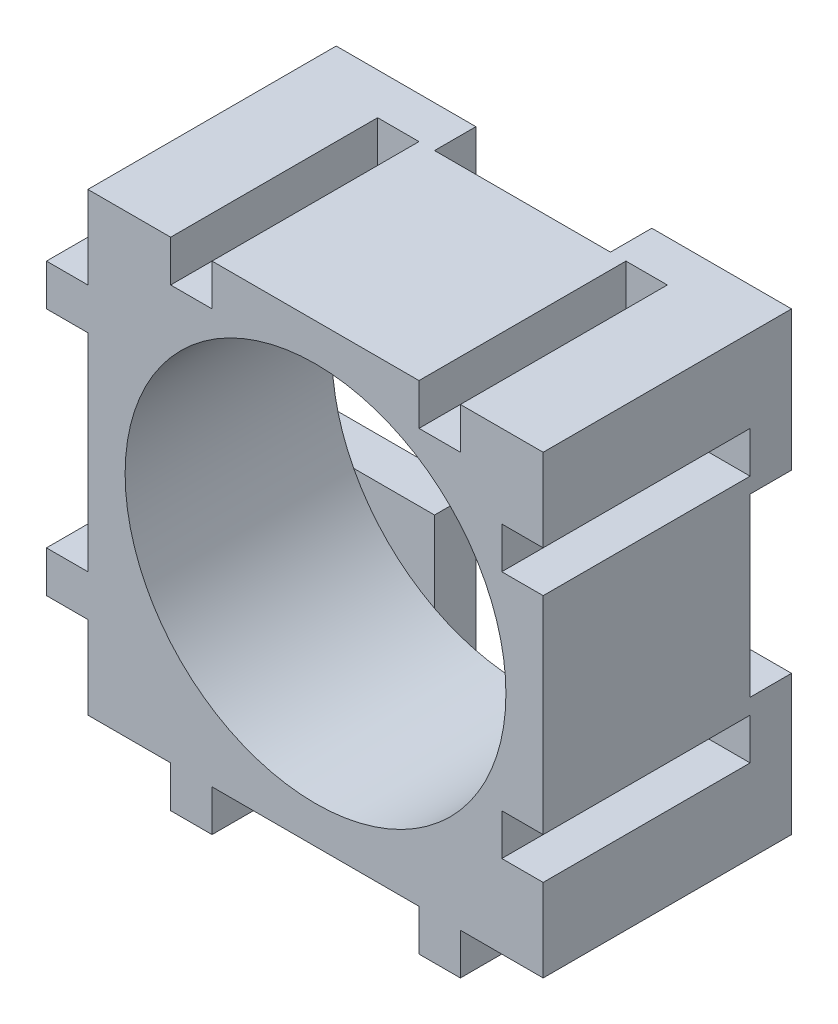
SolidWorks part; units mm, degrees
material "ABS"
ref_plane "Front Plane" through (0, 0, 0) normal (0, 0, 1) x (1, 0, 0)
ref_plane "Top Plane" through (0, 0, 0) normal (0, 1, 0) x (1, 0, 0)
ref_plane "Right Plane" through (0, 0, 0) normal (1, 0, 0) x (0, 0, -1)
sketch "Sketch1" plane through (0, 0, 0) normal (0, 0, 1) x (1, 0, 0)
  line L1 (-9.3991, 9.2441) -> (12.6009, 9.2441)
  line L2 (-9.3991, 9.2441) -> (-9.3991, -12.7559)
  line L3 (-9.3991, -12.7559) -> (12.6009, -12.7559)
  line L4 (12.6009, 9.2441) -> (12.6009, -12.7559)
  dimension "D1" = 22
  dimension "D2" = 22
extrude "Boss-Extrude1" add sketch "Sketch1" along normal blind 10
sketch "Sketch3" plane through (0, -12.7559, 0) normal (0, -1, 0) x (1, 0, 0)
  line L0 (-9.3991, 0) -> (12.6009, 0) construction
  line L1 (8.6009, 0) -> (6.6009, 0)
  line L2 (8.6009, 0) -> (8.6009, 10)
  line L3 (8.6009, 10) -> (6.6009, 10)
  line L4 (6.6009, 0) -> (6.6009, 10)
  line L5 (-9.3991, 10) -> (12.6009, 10) construction
  line L6 (-9.3991, 10) -> (-9.3991, 0) construction
  line L7 (-3.3991, 0) -> (-5.3991, 0)
  line L8 (-3.3991, 0) -> (-3.3991, 10)
  line L9 (-3.3991, 10) -> (-5.3991, 10)
  line L10 (-5.3991, 0) -> (-5.3991, 10)
  dimension "D1" = 2
  dimension "D2" = 2
  dimension "D3" = 10
  dimension "D4" = 4
extrude "Boss-Extrude2" add sketch "Sketch3" along normal blind 2
sketch "Sketch4" plane through (-9.3991, 0, 0) normal (-1, 0, 0) x (0, 0, 1)
  line L0 (0, 9.2441) -> (0, -12.7559) construction
  line L1 (0, 5.2441) -> (10, 5.2441)
  line L2 (0, 5.2441) -> (0, 3.2441)
  line L3 (0, 3.2441) -> (10, 3.2441)
  line L4 (10, 5.2441) -> (10, 3.2441)
  line L5 (10, 9.2441) -> (10, -12.7559) construction
  line L7 (0, -8.7559) -> (10, -8.7559)
  line L8 (0, -8.7559) -> (0, -6.7559)
  line L9 (0, -6.7559) -> (10, -6.7559)
  line L10 (10, -8.7559) -> (10, -6.7559)
  line L11 (10, 9.2441) -> (0, 9.2441) construction
  dimension "D1" = 10
  dimension "D2" = 4
  dimension "D3" = 2
  dimension "D4" = 2
extrude "Boss-Extrude3" add sketch "Sketch4" along normal blind 2
sketch "Sketch5" plane through (12.6009, 0, 0) normal (1, 0, 0) x (0, 0, -1)
  line L0 (0, -12.7559) -> (0, 9.2441) construction
  line L1 (0, 5.2441) -> (-10, 5.2441)
  line L2 (0, 5.2441) -> (0, 3.2441)
  line L3 (0, 3.2441) -> (-10, 3.2441)
  line L4 (-10, 5.2441) -> (-10, 3.2441)
  line L5 (-10, -12.7559) -> (-10, 9.2441) construction
  line L6 (-10, -12.7559) -> (0, -12.7559) construction
  line L7 (0, -6.7559) -> (-10, -6.7559)
  line L8 (0, -6.7559) -> (0, -8.7559)
  line L9 (0, -8.7559) -> (-10, -8.7559)
  line L10 (-10, -6.7559) -> (-10, -8.7559)
  dimension "D1" = 2
  dimension "D2" = 2
  dimension "D3" = 10
  dimension "D4" = 4
extrude "Cut-Extrude1" cut sketch "Sketch5" against normal blind 2
sketch "Sketch6" plane through (0, 9.2441, 0) normal (0, 1, 0) x (1, 0, 0)
  line L0 (12.6009, 0) -> (-9.3991, 0) construction
  line L1 (-5.3991, 0) -> (-3.3991, 0)
  line L2 (-5.3991, 0) -> (-5.3991, -10)
  line L3 (-5.3991, -10) -> (-3.3991, -10)
  line L4 (-3.3991, 0) -> (-3.3991, -10)
  line L5 (12.6009, -10) -> (-9.3991, -10) construction
  line L6 (12.6009, -10) -> (12.6009, 0) construction
  line L7 (6.6009, 0) -> (8.6009, 0)
  line L8 (6.6009, 0) -> (6.6009, -10)
  line L9 (6.6009, -10) -> (8.6009, -10)
  line L10 (8.6009, 0) -> (8.6009, -10)
  dimension "D1" = 2
  dimension "D2" = 2
  dimension "D3" = 10
  dimension "D4" = 4
extrude "Cut-Extrude2" cut sketch "Sketch6" against normal blind 2
sketch "Sketch7" plane through (0, 0, 10) normal (0, 0, 1) x (1, 0, 0)
  line L0 (12.6009, -6.7559) -> (12.6009, 3.2441) construction
  line L1 (-3.3991, -12.7559) -> (6.6009, -12.7559) construction
  circle A0 centre (1.6009, -1.7559) radius 9.2
  dimension "D1" = 18.4
  dimension "D3" = 11
  dimension "D2" = 11
extrude "Cut-Extrude3" cut sketch "Sketch7" against normal through all
sketch "Sketch8" plane through (0, 0, 0) normal (0, 0, -1) x (-1, 0, 0)
  line L1 (9.3991, 9.2441) -> (2.6491, 9.2441)
  line L2 (9.3991, 9.2441) -> (9.3991, 2.4941)
  line L3 (9.3991, 2.4941) -> (2.6491, 2.4941)
  line L4 (2.6491, 9.2441) -> (2.6491, 2.4941)
  line L5 (-12.6009, 9.2441) -> (-5.8509, 9.2441)
  line L6 (-12.6009, 9.2441) -> (-12.6009, 2.4941)
  line L7 (-12.6009, 2.4941) -> (-5.8509, 2.4941)
  line L8 (-5.8509, 9.2441) -> (-5.8509, 2.4941)
  line L9 (-12.6009, -12.7559) -> (-5.8509, -12.7559)
  line L10 (-12.6009, -12.7559) -> (-12.6009, -6.0059)
  line L11 (-12.6009, -6.0059) -> (-5.8509, -6.0059)
  line L12 (-5.8509, -12.7559) -> (-5.8509, -6.0059)
  line L13 (9.3991, -12.7559) -> (2.6491, -12.7559)
  line L14 (9.3991, -12.7559) -> (9.3991, -6.0059)
  line L15 (9.3991, -6.0059) -> (2.6491, -6.0059)
  line L16 (2.6491, -12.7559) -> (2.6491, -6.0059)
  dimension "D1" = 8.5
  dimension "D2" = 6.75
  dimension "D3" = 6.75
  dimension "D4" = 6.75
  dimension "D5" = 6.75
  dimension "D6" = 6.75
  dimension "D7" = 8.5
  dimension "D8" = 6.75
extrude "Boss-Extrude4" add sketch "Sketch8" along normal blind 2
sketch "Sketch9" plane through (0, 0, -2) normal (0, 0, -1) x (-1, 0, 0)
  line L1 (9.3991, -12.7559) -> (9.3991, -6.0059) construction
  line L2 (-12.6009, -6.0059) -> (-12.6009, -12.7559) construction
  line L4 (-12.6009, 9.2441) -> (-12.6009, 2.4941) construction
  line L5 (-5.8509, 9.2441) -> (-12.6009, 9.2441) construction
  line L6 (9.3991, 9.2441) -> (2.6491, 9.2441) construction
  line L8 (9.3991, 2.4941) -> (9.3991, 9.2441) construction
  line L9 (-12.6009, -12.7559) -> (-5.8509, -12.7559) construction
  line L10 (2.6491, -12.7559) -> (9.3991, -12.7559) construction
  circle A0 centre (7.3991, -10.7559) radius 1.5
  circle A1 centre (-10.6009, -10.7559) radius 1.5
  circle A2 centre (7.3991, 7.2441) radius 1.5
  circle A3 centre (-10.6009, 7.2441) radius 1.5
  dimension "D1" = 3
  dimension "D2" = 3
  dimension "D3" = 3
  dimension "D4" = 3
  dimension "D6" = 2
  dimension "D7" = 2
  dimension "D8" = 2
  dimension "D9" = 2
  dimension "D10" = 2
  dimension "D11" = 2
  dimension "D12" = 2
  dimension "D5" = 2
extrude "Cut-Extrude6" cut sketch "Sketch9" against normal blind 6
